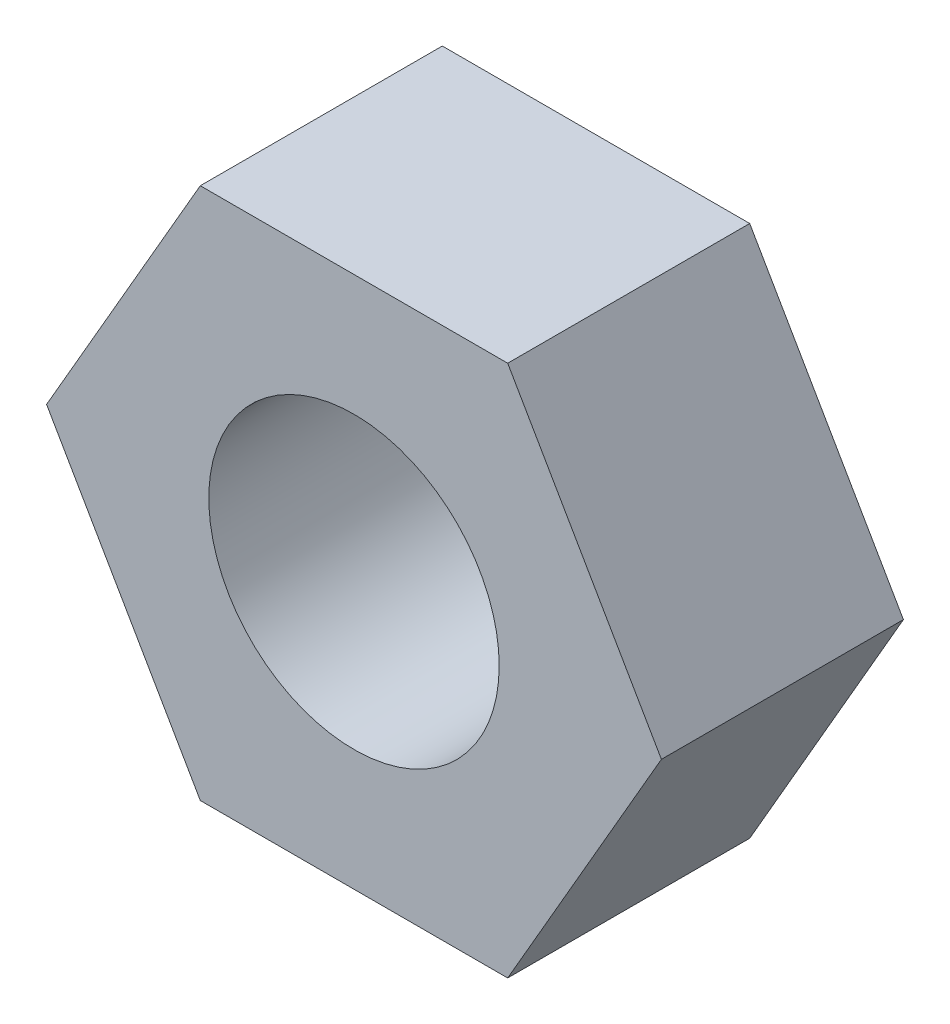
SolidWorks part; units mm, degrees
ref_plane "前视基准面" through (0, 0, 0) normal (0, 0, 1) x (1, 0, 0)
ref_plane "上视基准面" through (0, 0, 0) normal (0, 1, 0) x (1, 0, 0)
ref_plane "右视基准面" through (0, 0, 0) normal (1, 0, 0) x (0, 0, -1)
sketch "草图1" plane through (0, 0, 0) normal (0, 0, 1) x (1, 0, 0)
  line L1 (1.5877, 2.75) -> (-1.5877, 2.75)
  line L2 (-1.5877, 2.75) -> (-3.1754, 0)
  line L3 (-3.1754, 0) -> (-1.5877, -2.75)
  line L4 (-1.5877, -2.75) -> (1.5877, -2.75)
  line L5 (1.5877, -2.75) -> (3.1754, 0)
  line L6 (3.1754, 0) -> (1.5877, 2.75)
  circle A0 centre (0, 0) radius 2.75 construction
  circle A1 centre (0, 0) radius 1.5 construction
  dimension "D2" = 3
  dimension "D1" = 5.5
extrude "凸台-拉伸1" add sketch "草图1" along normal blind 2.5 contours L1 L2 L3 L4 L5 L6
sketch "草图2" plane through (0, 0, 2.5) normal (0, 0, 1) x (1, 0, 0)
  circle A0 centre (0, 0) radius 1.5
  dimension "D1" = 3
extrude "切除-拉伸1" cut sketch "草图2" against normal through all
